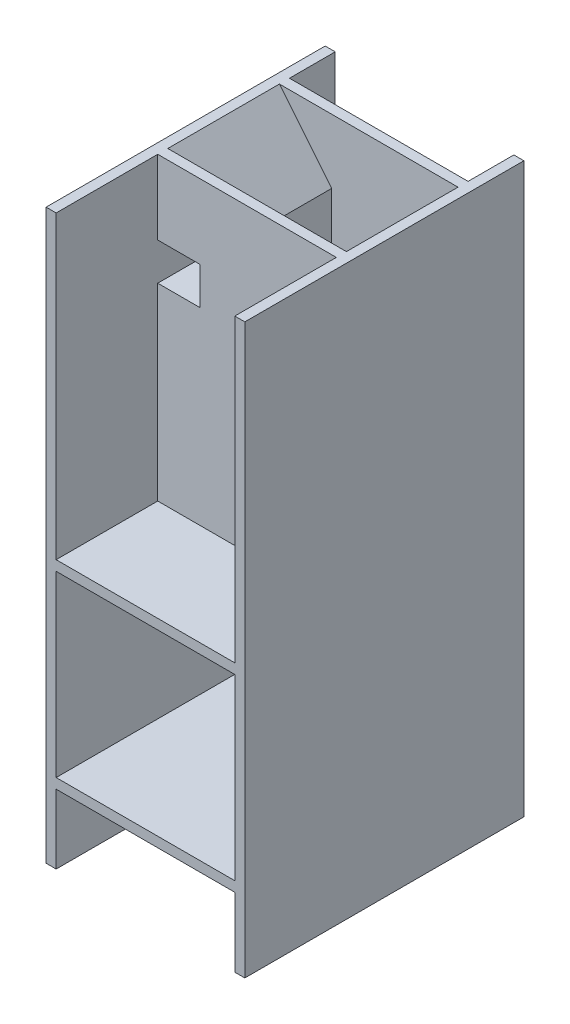
SolidWorks part; units mm, degrees
ref_plane "Front Plane" through (0, 0, 0) normal (0, 0, 1) x (1, 0, 0)
ref_plane "Top Plane" through (0, 0, 0) normal (0, 1, 0) x (1, 0, 0)
ref_plane "Right Plane" through (0, 0, 0) normal (1, 0, 0) x (0, 0, -1)
sketch "Sketch1" plane through (0, 0, 0) normal (0, 0, 1) x (1, 0, 0)
  line L0 (66.25, 263) -> (160, 378)
  line L5 (-178, -178) -> (178, -178)
  line L6 (-178, -178) -> (-178, 178)
  line L7 (-178, 178) -> (178, 178)
  line L8 (178, -178) -> (178, 178)
  line L9 (-178, -178) -> (178, 178) construction
  line L10 (-178, 178) -> (178, -178) construction
  line L11 (-160, -160) -> (160, -160)
  line L12 (-160, -160) -> (-160, 160)
  line L13 (-160, 160) -> (160, 160)
  line L14 (160, -160) -> (160, 160)
  line L15 (-160, -160) -> (160, 160) construction
  line L16 (-160, 160) -> (160, -160) construction
  line L17 (-66.25, 178) -> (66.25, 178)
  line L18 (-66.25, 178) -> (-66.25, 160)
  line L19 (-66.25, 160) -> (66.25, 160)
  line L20 (66.25, 178) -> (66.25, 160)
  line L21 (-66.25, -160) -> (66.25, -160)
  line L22 (-66.25, -160) -> (-66.25, -178)
  line L23 (-66.25, -178) -> (66.25, -178)
  line L24 (66.25, -160) -> (66.25, -178)
  line L25 (-178, -178) -> (178, -178)
  line L26 (-178, -178) -> (-178, -516)
  line L27 (-178, -516) -> (178, -516)
  line L28 (178, -178) -> (178, -516)
  line L29 (-160, -178) -> (160, -178)
  line L30 (-160, -178) -> (-160, -498)
  line L31 (-160, -498) -> (160, -498)
  line L32 (160, -178) -> (160, -498)
  line L33 (-178, -516) -> (178, -516)
  line L34 (-178, -516) -> (-178, -640)
  line L35 (-178, -640) -> (178, -640)
  line L36 (178, -516) -> (178, -640)
  line L37 (-160, -516) -> (160, -516)
  line L38 (-160, -516) -> (-160, -640)
  line L39 (-160, -640) -> (160, -640)
  line L40 (160, -516) -> (160, -640)
  line L41 (-178, 178) -> (178, 178)
  line L42 (-178, 178) -> (-178, 378)
  line L43 (-178, 378) -> (178, 378)
  line L44 (178, 178) -> (178, 378)
  line L45 (-160, 178) -> (160, 178)
  line L46 (-160, 178) -> (-160, 378)
  line L47 (-160, 378) -> (160, 378)
  line L48 (160, 178) -> (160, 378)
  line L53 (-160, 178) -> (-84.25, 178)
  line L54 (-160, 178) -> (-160, 245)
  line L55 (160, 178) -> (66.25, 178)
  line L56 (160, 178) -> (160, 263)
  line L57 (160, 263) -> (66.25, 263)
  line L58 (66.25, 178) -> (66.25, 263)
  line L59 (-160, 178) -> (-66.25, 178)
  line L60 (-160, 178) -> (-160, 263)
  line L61 (-160, 263) -> (-66.25, 263)
  line L62 (-66.25, 178) -> (-66.25, 263)
  line L63 (160, 178) -> (84.25, 178)
  line L64 (160, 178) -> (160, 245)
  line L65 (160, 245) -> (84.25, 245)
  line L66 (84.25, 178) -> (84.25, 245)
  line L67 (-160, 178) -> (-84.25, 178)
  line L68 (-160, 178) -> (-160, 245)
  line L69 (-160, 245) -> (-84.25, 245)
  line L70 (-84.25, 178) -> (-84.25, 245)
  line L71 (84.25, 263) -> (160, 355.92)
  line L72 (-66.25, 263) -> (-160, 378)
  line L73 (-84.25, 263) -> (-160, 355.92)
  line L74 (-160, 355.92) -> (-160, 378)
  line L75 (-66.25, 263) -> (-84.25, 263)
  line L76 (160, 355.92) -> (160, 378)
  line L77 (84.25, 263) -> (66.25, 263)
  line L78 (66.25, 160) -> (160, 66.25)
  line L79 (84.25, 160) -> (160, 84.25)
  line L80 (160, 84.25) -> (160, 66.25)
  line L81 (84.25, 160) -> (66.25, 160)
  line L82 (-66.25, 160) -> (-160, 66.25)
  line L83 (-160, 66.25) -> (-160, 84.25)
  line L84 (-160, 84.25) -> (-84.25, 160)
  line L85 (-84.25, 160) -> (-66.25, 160)
  line L86 (66.25, -160) -> (160, -66.25)
  line L87 (160, -66.25) -> (160, -84.25)
  line L88 (160, -84.25) -> (84.25, -160)
  line L89 (84.25, -160) -> (66.25, -160)
  line L90 (-66.25, -160) -> (-160, -66.25)
  line L91 (-160, -66.25) -> (-160, -84.25)
  line L92 (-160, -84.25) -> (-84.25, -160)
  line L93 (-84.25, -160) -> (-66.25, -160)
  point P0 (0, 0)
  point P1 (0, 0)
  point P7 (0, 0)
  dimension "D1" = 356
  dimension "D2" = 356
  dimension "D3" = 320
  dimension "D4" = 320
  dimension "D5" = 111.75
  dimension "D6" = 111.75
  dimension "D7" = 111.75
  dimension "D8" = 111.75
  dimension "D9" = 338
  dimension "D10" = 320
  dimension "D11" = 124
  dimension "D12" = 200
  dimension "D13" = 85
  dimension "D14" = 85
  dimension "D15" = 18
  dimension "D16" = 18
  dimension "D17" = 18
  dimension "D18" = 18
extrude "Boss-Extrude4" add sketch "Sketch1" along normal mid plane 300 contours L48 L41 L44 L43 L56 | L7 L66 L65 L56 L57 L58 | L70 L45 L62 L61 L46 L69 | L7 L46 L43 L42 | L22 L11 L12 L13 L18 L45 L41 L7 L6 L5 L25 | L11 L24 L5 L25 L8 L41 L55 L7 L20 L13 L14 | L79 L13 L78 L14 | L84 L12 L82 L13 | L88 L14 L86 L11 | L12 L92 L11 L90 | L25 L32 L31 L30 L5 L26 L27 L33 L28 | L27 L40 L35 L36 | L38 L27 L34 L35
ref_plane "Plane1" through (0, 263, 0) normal (0, -1, 0) x (-1, 0, 0)
sketch "Sketch12" plane through (0, 263, 0) normal (0, -1, 0) x (-1, 0, 0)
  line L0 (160, -150) -> (160, 150) construction
  line L1 (160, 68) -> (-160, 68)
  line L2 (160, 68) -> (160, 50)
  line L3 (160, 50) -> (-160, 50)
  line L4 (-160, 68) -> (-160, 50)
  line L5 (-160, -150) -> (-160, 150) construction
  dimension "D1" = 18
  dimension "D2" = 100
extrude "Boss-Extrude6" add sketch "Sketch12" against normal blind 115
ref_plane "Plane5" through (0, 0, 150) normal (0, 0, 1) x (1, 0, 0)
sketch "Sketch13" plane through (0, 0, 150) normal (0, 0, 1) x (1, 0, 0)
  line L0 (-160, 378) -> (-66.25, 263)
  line L1 (-66.25, 263) -> (-84.25, 263)
  line L2 (-160, 263) -> (-66.25, 263) construction
  line L3 (-84.25, 263) -> (-160, 355.92)
  line L4 (-160, 263) -> (-160, 378) construction
  line L5 (-160, 355.92) -> (-160, 378)
  dimension "D1" = 18
extrude "Boss-Extrude8" add sketch "Sketch13" against normal blind 200
sketch "Sketch15" plane through (0, 0, 150) normal (0, 0, 1) x (1, 0, 0)
  line L0 (160, 378) -> (66.25, 263)
  line L1 (66.25, 263) -> (84.25, 263)
  line L2 (160, 263) -> (66.25, 263) construction
  line L3 (84.25, 263) -> (160, 355.92)
  line L4 (160, 263) -> (160, 378) construction
  line L5 (160, 355.92) -> (160, 378)
  dimension "D1" = 18
  dimension "D2" = 22.08
extrude "Boss-Extrude9" add sketch "Sketch15" against normal blind 200
sketch "Sketch26" plane through (0, 0, 150) normal (0, 0, 1) x (1, 0, 0)
  line L1 (-178, 378) -> (-160, 378)
  line L2 (-178, 378) -> (-178, -640)
  line L3 (-178, -640) -> (-160, -640)
  line L4 (-160, 378) -> (-160, -640)
extrude "Boss-Extrude30" add sketch "Sketch26" along normal blind 200
sketch "Sketch27" plane through (0, 0, 150) normal (0, 0, 1) x (1, 0, 0)
  line L1 (178, 378) -> (160, 378)
  line L2 (178, 378) -> (178, -640)
  line L3 (178, -640) -> (160, -640)
  line L4 (160, 378) -> (160, -640)
extrude "Boss-Extrude31" add sketch "Sketch27" along normal blind 200
sketch "Sketch28" plane through (0, 0, 150) normal (0, 0, 1) x (1, 0, 0)
  line L1 (-160, -160) -> (160, -160)
  line L2 (-160, -160) -> (-160, -178)
  line L3 (-160, -178) -> (160, -178)
  line L4 (160, -160) -> (160, -178)
extrude "Boss-Extrude32" add sketch "Sketch28" along normal blind 200
sketch "Sketch29" plane through (0, 0, 150) normal (0, 0, 1) x (1, 0, 0)
  line L1 (-160, -498) -> (160, -498)
  line L2 (-160, -498) -> (-160, -516)
  line L3 (-160, -516) -> (160, -516)
  line L4 (160, -498) -> (160, -516)
extrude "Boss-Extrude33" add sketch "Sketch29" along normal blind 200
sketch "Sketch30" plane through (0, 0, 150) normal (0, 0, 1) x (1, 0, 0)
  line L0 (160, -160) -> (-160, -160) construction
  line L1 (-160, 178) -> (160, 178)
  line L2 (-160, 178) -> (-160, -160)
  line L3 (-160, -160) -> (160, -160)
  line L4 (160, 178) -> (160, -160)
  line L5 (160, 378) -> (160, -160) construction
sketch "Sketch31" plane through (0, 0, 150) normal (0, 0, 1) x (1, 0, 0)
  line L1 (-160, 178) -> (160, 178)
  line L2 (-160, 178) -> (-160, -160)
  line L3 (-160, -160) -> (160, -160)
  line L4 (160, 178) -> (160, -160)
sketch "Sketch32" plane through (0, 0, 150) normal (0, 0, 1) x (1, 0, 0)
  line L0 (160, 378) -> (-160, 378) construction
  line L1 (-160, 378) -> (160, 378)
  line L2 (-160, 378) -> (-160, -160)
  line L3 (-160, -160) -> (160, -160)
  line L4 (160, 378) -> (160, -160)
  line L5 (-66.25, 263) -> (-160, 378) construction
extrude "Boss-Extrude35" add sketch "Sketch32" along normal blind 18
sketch "Sketch33" plane through (0, 0, -150) normal (0, 0, -1) x (-1, 0, 0)
  line L0 (178, 378) -> (178, -640) construction
  line L1 (-178, 378) -> (178, 378)
  line L2 (-178, 378) -> (-178, -178)
  line L3 (-178, -178) -> (178, -178)
  line L4 (178, 378) -> (178, -178)
sketch "Sketch34" plane through (0, 0, 150) normal (0, 0, -1) x (-1, 0, 0)
  line L1 (-160, 245) -> (-84.25, 245)
  line L2 (-160, 245) -> (-160, 178)
  line L3 (-160, 178) -> (-84.25, 178)
  line L4 (-84.25, 245) -> (-84.25, 178)
extrude "Cut-Extrude1" cut sketch "Sketch34" against normal blind 18
sketch "Sketch35" plane through (0, 0, 150) normal (0, 0, -1) x (-1, 0, 0)
  line L0 (160, 178) -> (84.25, 178) construction
  line L1 (84.25, 245) -> (160, 245)
  line L2 (84.25, 245) -> (84.25, 178)
  line L3 (84.25, 178) -> (160, 178)
  line L4 (160, 245) -> (160, 178)
extrude "Cut-Extrude2" cut sketch "Sketch35" against normal blind 18
sketch "Sketch46" plane through (0, 263, 0) normal (0, 1, 0) x (1, 0, 0)
  line L1 (66.25, 150) -> (160, 150)
  line L2 (66.25, 150) -> (66.25, 68)
  line L3 (66.25, 68) -> (160, 68)
  line L4 (160, 150) -> (160, 68)
extrude "Cut-Extrude14" cut sketch "Sketch46" against normal blind 85
sketch "Sketch47" plane through (0, 263, 0) normal (0, 1, 0) x (1, 0, 0)
  line L1 (-160, 150) -> (-66.25, 150)
  line L2 (-160, 150) -> (-160, 68)
  line L3 (-160, 68) -> (-66.25, 68)
  line L4 (-66.25, 150) -> (-66.25, 68)
extrude "Cut-Extrude15" cut sketch "Sketch47" against normal blind 85
sketch "Sketch48" plane through (0, 0, -68) normal (0, 0, -1) x (-1, 0, 0)
  line L0 (66.25, 178) -> (66.25, 263) construction
  line L1 (-66.25, 263) -> (66.25, 263)
  line L2 (-66.25, 263) -> (-66.25, 178)
  line L3 (-66.25, 178) -> (66.25, 178)
  line L4 (66.25, 263) -> (66.25, 178)
  line L5 (66.25, 263) -> (66.25, 160) construction
extrude "Boss-Extrude44" add sketch "Sketch48" against normal blind 18
sketch "Sketch51" plane through (0, 0, -150) normal (0, 0, -1) x (-1, 0, 0)
  line L1 (-66.25, 178) -> (66.25, 178)
  line L2 (-66.25, 178) -> (-66.25, 160)
  line L3 (-66.25, 160) -> (66.25, 160)
  line L4 (66.25, 178) -> (66.25, 160)
extrude "Boss-Extrude46" add sketch "Sketch51" against normal blind 100
